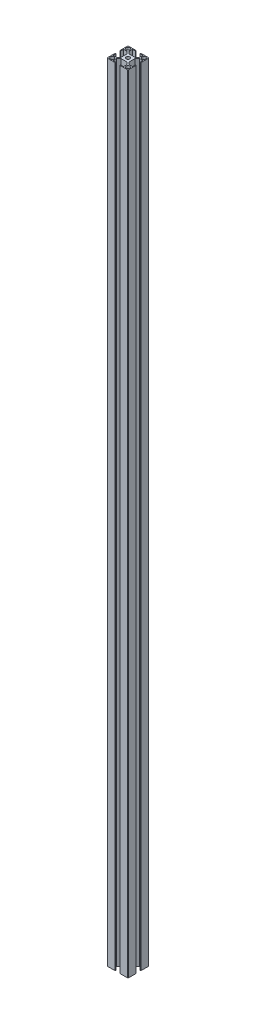
SolidWorks part; units mm, degrees
ref_plane "Front Plane" through (0, 0, 0) normal (0, 0, 1) x (1, 0, 0)
ref_plane "Top Plane" through (0, 0, 0) normal (0, 1, 0) x (1, 0, 0)
ref_plane "Right Plane" through (0, 0, 0) normal (1, 0, 0) x (0, 0, -1)
sketch "Sketch1" plane through (0, 0, 0) normal (0, 1, 0) x (1, 0, 0)
  line L0 (20, 19) -> (20, -19)
  line L1 (-19, -20) -> (19, -20)
  line L2 (-20, -19) -> (-20, 19)
  line L3 (-19, 20) -> (19, 20)
  line L5 (-20, -20) -> (20, 0) construction
  line L6 (-20, 20) -> (20, 0) construction
  line L7 (-20, 20) -> (20, -20) construction
  line L8 (20, 20) -> (-20, -20) construction
  line L9 (-20, 0) -> (20, 0) construction
  line L10 (-10, -18.5) -> (10, -18.5)
  line L11 (10, -18.5) -> (10, -11.825)
  line L12 (10, -11.825) -> (5.875, -7.7)
  line L13 (5.875, -7.7) -> (-5.875, -7.7)
  line L14 (-5.875, -7.7) -> (-10, -11.825)
  line L15 (-10, -11.825) -> (-10, -18.5)
  line L16 (-11.825, -10) -> (-18.5, -10)
  line L17 (-7.7, -5.875) -> (-11.825, -10)
  line L18 (-7.7, 5.875) -> (-7.7, -5.875)
  line L19 (-11.825, 10) -> (-7.7, 5.875)
  line L20 (-18.5, 10) -> (-11.825, 10)
  line L21 (-18.5, -10) -> (-18.5, 10)
  line L22 (-10, 11.825) -> (-10, 18.5)
  line L23 (-5.875, 7.7) -> (-10, 11.825)
  line L24 (5.875, 7.7) -> (-5.875, 7.7)
  line L25 (10, 11.825) -> (5.875, 7.7)
  line L26 (10, 18.5) -> (10, 11.825)
  line L27 (-10, 18.5) -> (10, 18.5)
  line L28 (0, 20) -> (0, -20) construction
  line L29 (18.5, -10) -> (18.5, 10)
  line L30 (18.5, 10) -> (11.825, 10)
  line L31 (11.825, 10) -> (7.7, 5.875)
  line L32 (7.7, 5.875) -> (7.7, -5.875)
  line L33 (7.7, -5.875) -> (11.825, -10)
  line L34 (11.825, -10) -> (18.5, -10)
  line L35 (15.1625, -10) -> (15.1625, -15.1625) construction
  arc A0 (-19, -20) -> (-20, -19) centre (-19, -19) cw
  arc A1 (20, -19) -> (19, -20) centre (19, -19) cw
  arc A2 (20, 19) -> (19, 20) centre (19, 19) ccw
  arc A3 (-19, 20) -> (-20, 19) centre (-19, 19) ccw
  circle A4 centre (15.1625, -15.1625) radius 3.5
  circle A5 centre (-15.1625, -15.1625) radius 3.5
  circle A6 centre (-15.1625, 15.1625) radius 3.5
  circle A7 centre (15.1625, 15.1625) radius 3.5
  circle A8 centre (0, 0) radius 3.5
  point P30 (0, 0)
  point P31 (0, 18.5)
  point P59 (0, 0)
  dimension "D7" = 1
  dimension "D8" = 7
  dimension "D10" = 7
  dimension "D1" = 40
  dimension "D2" = 40
  dimension "D3" = 10.8
  dimension "D4" = 11.75
  dimension "D5" = 20
  dimension "D6" = 1.5
  dimension "D9" = 4
extrude "Boss-Extrude1" add sketch "Sketch1" along normal blind 1500
sketch "Sketch2" plane through (0, 1500, 0) normal (0, 1, 0) x (1, 0, 0)
  line L0 (-4.65, 20) -> (-4.65, 19.35)
  line L1 (19, 20) -> (-19, 20) construction
  line L2 (-4.55, 19.25) -> (-4.25, 19.25)
  line L3 (-4.15, 19.15) -> (-4.15, 18.5)
  line L4 (10, 18.5) -> (-10, 18.5) construction
  line L5 (0, 20) -> (0, 18.5) construction
  line L6 (4.15, 19.15) -> (4.15, 18.5)
  line L7 (4.55, 19.25) -> (4.25, 19.25)
  line L8 (4.65, 20) -> (4.65, 19.35)
  line L9 (-4.65, 20) -> (4.65, 20)
  line L10 (-4.15, 18.5) -> (4.15, 18.5)
  line L11 (20, 4.65) -> (19.35, 4.65)
  line L12 (19.25, 4.55) -> (19.25, 4.25)
  line L13 (19.15, 4.15) -> (18.5, 4.15)
  line L14 (19.15, -4.15) -> (18.5, -4.15)
  line L15 (19.25, -4.55) -> (19.25, -4.25)
  line L16 (20, -4.65) -> (19.35, -4.65)
  line L17 (20, 4.65) -> (20, -4.65)
  line L18 (18.5, 4.15) -> (18.5, -4.15)
  line L19 (20, 0) -> (18.5, 0) construction
  line L20 (4.65, -20) -> (4.65, -19.35)
  line L21 (4.55, -19.25) -> (4.25, -19.25)
  line L22 (4.15, -19.15) -> (4.15, -18.5)
  line L23 (-4.15, -19.15) -> (-4.15, -18.5)
  line L24 (-4.55, -19.25) -> (-4.25, -19.25)
  line L25 (-4.65, -20) -> (-4.65, -19.35)
  line L26 (4.65, -20) -> (-4.65, -20)
  line L27 (4.15, -18.5) -> (-4.15, -18.5)
  line L28 (0, -20) -> (0, -18.5) construction
  line L29 (-20, -4.65) -> (-19.35, -4.65)
  line L30 (-19.25, -4.55) -> (-19.25, -4.25)
  line L31 (-19.15, -4.15) -> (-18.5, -4.15)
  line L32 (-19.15, 4.15) -> (-18.5, 4.15)
  line L33 (-19.25, 4.55) -> (-19.25, 4.25)
  line L34 (-20, 4.65) -> (-19.35, 4.65)
  line L35 (-20, -4.65) -> (-20, 4.65)
  line L36 (-18.5, -4.15) -> (-18.5, 4.15)
  line L37 (-20, 0) -> (-18.5, 0) construction
  arc A0 (4.55, 19.25) -> (4.65, 19.35) centre (4.55, 19.35) ccw
  arc A1 (4.25, 19.25) -> (4.15, 19.15) centre (4.25, 19.15) ccw
  arc A2 (-4.15, 19.15) -> (-4.25, 19.25) centre (-4.25, 19.15) ccw
  arc A3 (-4.65, 19.35) -> (-4.55, 19.25) centre (-4.55, 19.35) ccw
  arc A4 (19.25, -4.55) -> (19.35, -4.65) centre (19.35, -4.55) ccw
  arc A5 (19.25, -4.25) -> (19.15, -4.15) centre (19.15, -4.25) ccw
  arc A6 (19.15, 4.15) -> (19.25, 4.25) centre (19.15, 4.25) ccw
  arc A7 (19.35, 4.65) -> (19.25, 4.55) centre (19.35, 4.55) ccw
  arc A8 (-4.55, -19.25) -> (-4.65, -19.35) centre (-4.55, -19.35) ccw
  arc A9 (-4.25, -19.25) -> (-4.15, -19.15) centre (-4.25, -19.15) ccw
  arc A10 (4.15, -19.15) -> (4.25, -19.25) centre (4.25, -19.15) ccw
  arc A11 (4.65, -19.35) -> (4.55, -19.25) centre (4.55, -19.35) ccw
  arc A12 (-19.25, 4.55) -> (-19.35, 4.65) centre (-19.35, 4.55) ccw
  arc A13 (-19.25, 4.25) -> (-19.15, 4.15) centre (-19.15, 4.25) ccw
  arc A14 (-19.15, -4.15) -> (-19.25, -4.25) centre (-19.15, -4.25) ccw
  arc A15 (-19.35, -4.65) -> (-19.25, -4.55) centre (-19.35, -4.55) ccw
  point P16 (4.65, 19.25)
  point P19 (4.15, 19.25)
  point P22 (-4.15, 19.25)
  point P25 (-4.65, 19.25)
  point P83 (0, 0)
  dimension "D4" = 0.1
  dimension "D1" = 0.75
  dimension "D2" = 0.5
  dimension "D3" = 4.15
  dimension "D5" = 4
extrude "Cut-Extrude1" cut sketch "Sketch2" against normal through all
